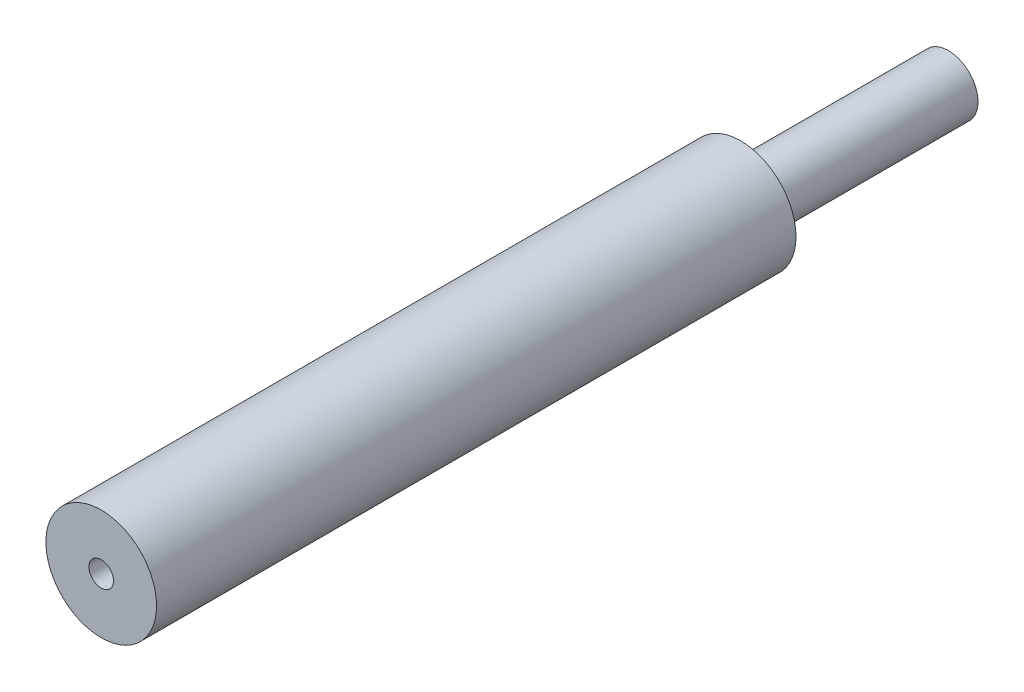
SolidWorks part; units mm, degrees
material "AISI 316 Annealed Stainless Steel Bar (SS)"
ref_plane "Front Plane" through (0, 0, 0) normal (0, 0, 1) x (1, 0, 0)
ref_plane "Top Plane" through (0, 0, 0) normal (0, 1, 0) x (1, 0, 0)
ref_plane "Right Plane" through (0, 0, 0) normal (1, 0, 0) x (0, 0, -1)
sketch "Sketch1" plane through (0, 0, 0) normal (0, 0, 1) x (1, 0, 0)
  circle A0 centre (0, 0) radius 1.2
  circle A1 centre (0, 0) radius 0.5
  dimension "D1" = 1
  dimension "D2" = 2.4
extrude "Boss-Extrude1" add sketch "Sketch1" along normal blind 8.45
sketch "Sketch2" plane through (0, 0, 8.45) normal (0, 0, 1) x (1, 0, 0)
  circle A0 centre (0, 0) radius 0.5
  circle A1 centre (0, 0) radius 2.25
  dimension "D1" = 1
  dimension "D2" = 4.5
extrude "Boss-Extrude2" add sketch "Sketch2" along normal blind 26
